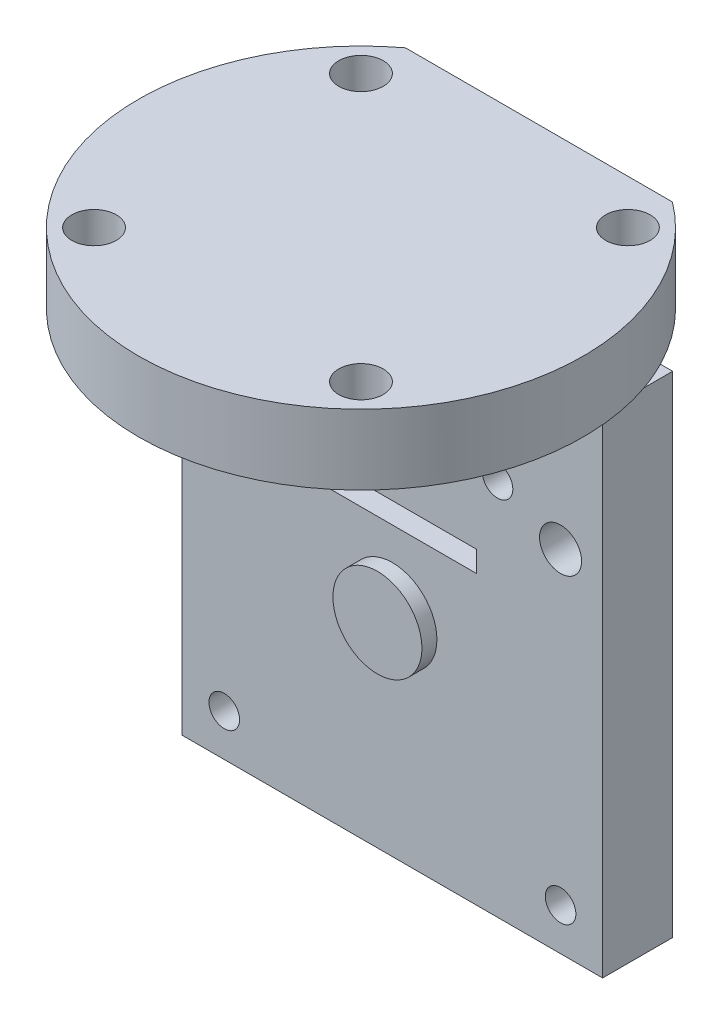
SolidWorks part; units mm, degrees
material "Copper"
ref_plane "Front Plane" through (0, 0, 0) normal (0, 0, 1) x (1, 0, 0)
ref_plane "Top Plane" through (0, 0, 0) normal (0, 1, 0) x (1, 0, 0)
ref_plane "Right Plane" through (0, 0, 0) normal (1, 0, 0) x (0, 0, -1)
sketch "Sketch1" plane through (0, 0, 0) normal (0, 1, 0) x (1, 0, 0)
  line L0 (-15.875, 0) -> (15.875, 0) construction
  line L1 (0, -15.875) -> (0, 12.7) construction
  line L2 (9.525, 12.7) -> (-9.525, 12.7)
  line L3 (0, 0) -> (11.1125, 0) construction
  line L4 (-9.525, 9.525) -> (-9.525, -9.525) construction
  line L5 (11.1125, 11.337) -> (11.1125, -11.337) construction
  line L6 (9.525, 9.525) -> (9.525, -9.525) construction
  arc A0 (-9.525, 12.7) -> (9.525, 12.7) centre (0, 0) ccw
  circle A1 centre (-12.7, 0) radius 1.5875
  circle A2 centre (12.7, 0) radius 1.5875
  circle A3 centre (0, -12.7) radius 1.5875
  circle A5 centre (9.525, 9.525) radius 1.5875
  circle A6 centre (-9.525, 9.525) radius 1.5875
  circle A7 centre (-9.525, -9.525) radius 1.5875
  circle A9 centre (9.525, -9.525) radius 1.5875
  dimension "D1" = 19.05
  dimension "D2" = 3.175
  dimension "D3" = 3.175
  dimension "D4" = 3.175
  dimension "D7" = 3.175
  dimension "D9" = 3.175
  dimension "D10" = 3.175
  dimension "D12" = 3.175
  dimension "D14" = 3.175
  dimension "D15" = 3.175
  dimension "D5" = 3.175
  dimension "D6" = 3.175
  dimension "D8" = 3.175
  dimension "D11" = 3.175
  dimension "D13" = 3.175
  dimension "D16" = 3.175
  dimension "D17" = 19.05
sketch "Sketch2" plane through (0, 0, 0) normal (0, 1, 0) x (1, 0, 0)
  circle A0 centre (-12.7, 0) radius 1.5875
  circle A1 centre (0, -12.7) radius 1.5875
  circle A2 centre (12.7, 0) radius 1.5875
extrude "Boss-Extrude3" add sketch "Sketch1" along normal blind 5
extrude "Boss-Extrude4" add sketch "Sketch2" along normal blind 5
sketch "Sketch3" plane through (0, 0, 0) normal (0, 0, 1) x (1, 0, 0)
  line L0 (-15.875, 5) -> (-15.875, 0) construction
  line L1 (-15, 0) -> (15, 0)
  line L2 (-15, 0) -> (-15, -35)
  line L3 (-15, -35) -> (15, -35)
  line L4 (15, 0) -> (15, -35)
  line L5 (15.875, 0) -> (15.875, 5) construction
  line L6 (-15.875, 0) -> (15.875, 0) construction
  line L7 (-15, -17.5) -> (15, -17.5) construction
  line L8 (0, -35) -> (0, 0) construction
  line L10 (-6, -13) -> (6, -13)
  line L11 (-6, -13) -> (-6, -14.5)
  line L12 (-6, -14.5) -> (6, -14.5)
  line L13 (6, -13) -> (6, -14.5)
  circle A0 centre (-7.5, -8) radius 1.0922
  circle A1 centre (7.5, -8) radius 1.0922
  circle A2 centre (0, -20) radius 3.175
  circle A3 centre (-12, -32) radius 1.0922
  circle A4 centre (12, -32) radius 1.0922
  point P24 (0, -17.5)
  dimension "D9" = 2.1844
  dimension "D10" = 2.1844
  dimension "D15" = 6.35
  dimension "D22" = 2.1844
  dimension "D23" = 2.1844
  dimension "D1" = 0.875
  dimension "D2" = 0.875
  dimension "D3" = 0
  dimension "D4" = 35
  dimension "D5" = 7.5
  dimension "D6" = 7.5
  dimension "D7" = 8
  dimension "D8" = 8
  dimension "D11" = 13
  dimension "D12" = 1.5
  dimension "D13" = 6
  dimension "D14" = 12
  dimension "D16" = 15
  dimension "D17" = 20
  dimension "D18" = 3
  dimension "D19" = 3
  dimension "D20" = 3
  dimension "D21" = 3
extrude "Boss-Extrude9" add sketch "Sketch3" against normal blind 5 from offset 2.245 offset against normal yes
sketch "Sketch11" plane through (0, 0, -7.245) normal (0, 0, -1) x (-1, 0, 0)
  circle A0 centre (0, -20) radius 3.175
extrude "Boss-Extrude10" add sketch "Sketch11" against normal blind 6.07
sketch "Sketch12" plane through (0, 0, -7.245) normal (0, 0, -1) x (-1, 0, 0)
  line L0 (-14.1254, 0) -> (14.1254, 0) construction
  line L1 (-15, -35) -> (-15, 0) construction
  line L2 (15, 0) -> (15, -35) construction
  circle A0 centre (-12, -10) radius 1.5
  circle A1 centre (0, -10) radius 1.5
  circle A2 centre (12, -10) radius 1.5
  dimension "D5" = 3
  dimension "D7" = 3
  dimension "D9" = 3
  dimension "D1" = 10
  dimension "D2" = 10
  dimension "D3" = 10
  dimension "D4" = 15
  dimension "D6" = 3
  dimension "D8" = 3
extrude "Cut-Extrude2" cut sketch "Sketch12" against normal up to surface (5 mm away) up to face at (13.0922, -32, -2.245)
